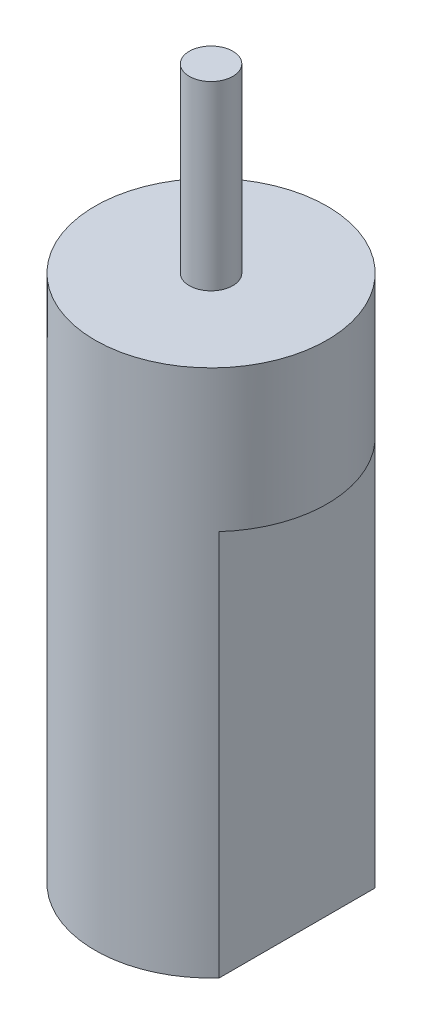
SolidWorks part; units mm, degrees
ref_plane "Front Plane" through (0, 0, 0) normal (0, 0, 1) x (1, 0, 0)
ref_plane "Top Plane" through (0, 0, 0) normal (0, 1, 0) x (1, 0, 0)
ref_plane "Right Plane" through (0, 0, 0) normal (1, 0, 0) x (0, 0, -1)
other "Bounding Box"
ref_plane "Default Plane" through (13.8565, 3.175, 6.7999) normal (0, -1, 0) x (-1, 0, 0)
sketch "Sketch1" plane through (0, 0, 0) normal (0, 1, 0) x (1, 0, 0)
  circle A1 centre (0, 0) radius 8
  dimension "D1" = 16
extrude "Boss-Extrude1" add sketch "Sketch1" along normal blind 36.4236
sketch "Sketch2" plane through (0, 0, 0) normal (0, -1, 0) x (1, 0, 0)
  line L0 (5.9309, 5.3688) -> (5.9309, -5.3688)
  line L1 (-5.9309, 5.3688) -> (-5.9309, -5.3688)
  arc A0 (5.9309, -5.3688) -> (5.9309, 5.3688) centre (0, 0) ccw
  arc A1 (-5.9309, 5.3688) -> (-5.9309, -5.3688) centre (0, 0) ccw
  circle A2 centre (0, 0) radius 8 construction
  point P1 (-4.9447, 7.5396)
  point P9 (4.0316, 6.9098)
  dimension "D1" = 11.8618
extrude "Cut-Extrude1" cut sketch "Sketch2" against normal offset from surface (26.6446 mm away) 9.779 up to face at (0, 36.4236, 8)
sketch "Sketch3" plane through (0, 36.4236, 0) normal (0, 1, 0) x (1, 0, 0)
  circle A0 centre (0, 0) radius 1.5
  dimension "D1" = 3
extrude "Boss-Extrude2" add sketch "Sketch3" along normal blind 12.4968
